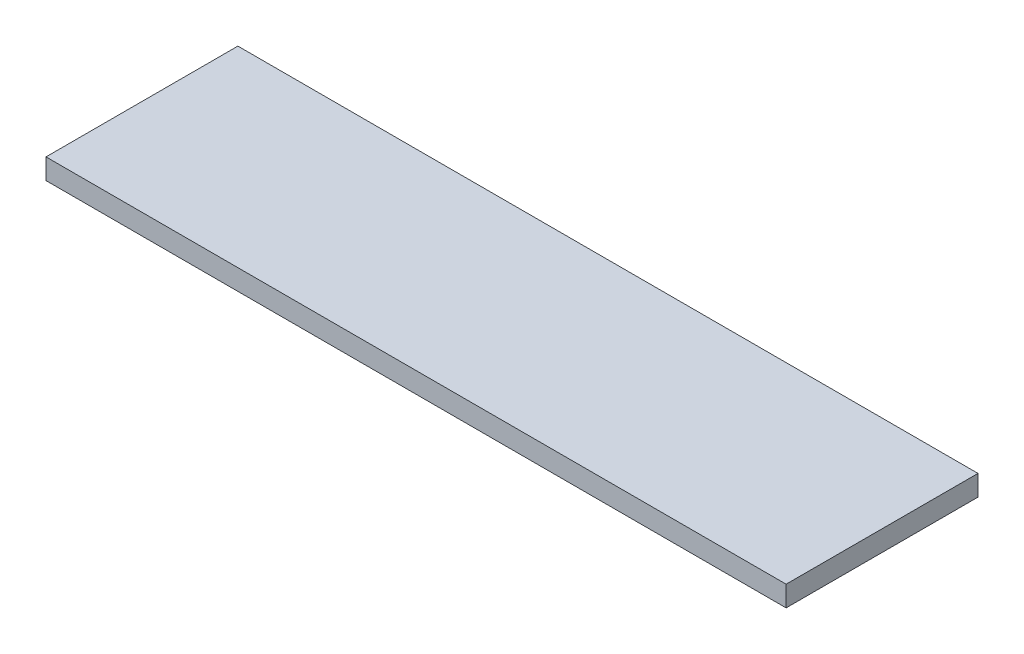
SolidWorks part; units mm, degrees
material "Pine"
ref_plane "Front Plane" through (0, 0, 0) normal (0, 0, 1) x (1, 0, 0)
ref_plane "Top Plane" through (0, 0, 0) normal (0, 1, 0) x (1, 0, 0)
ref_plane "Right Plane" through (0, 0, 0) normal (1, 0, 0) x (0, 0, -1)
sketch "Sketch1" plane through (0, 0, 0) normal (0, 1, 0) x (1, 0, 0)
  line L1 (-342.9, 88.9) -> (342.9, 88.9)
  line L2 (-342.9, 88.9) -> (-342.9, -88.9)
  line L3 (-342.9, -88.9) -> (342.9, -88.9)
  line L4 (342.9, 88.9) -> (342.9, -88.9)
  line L5 (-342.9, 88.9) -> (342.9, -88.9) construction
  line L6 (-342.9, -88.9) -> (342.9, 88.9) construction
  point P0 (0, 0)
  dimension "D1" = 685.8
  dimension "D2" = 177.8
extrude "Boss-Extrude1" add sketch "Sketch1" along normal mid plane 19.05
